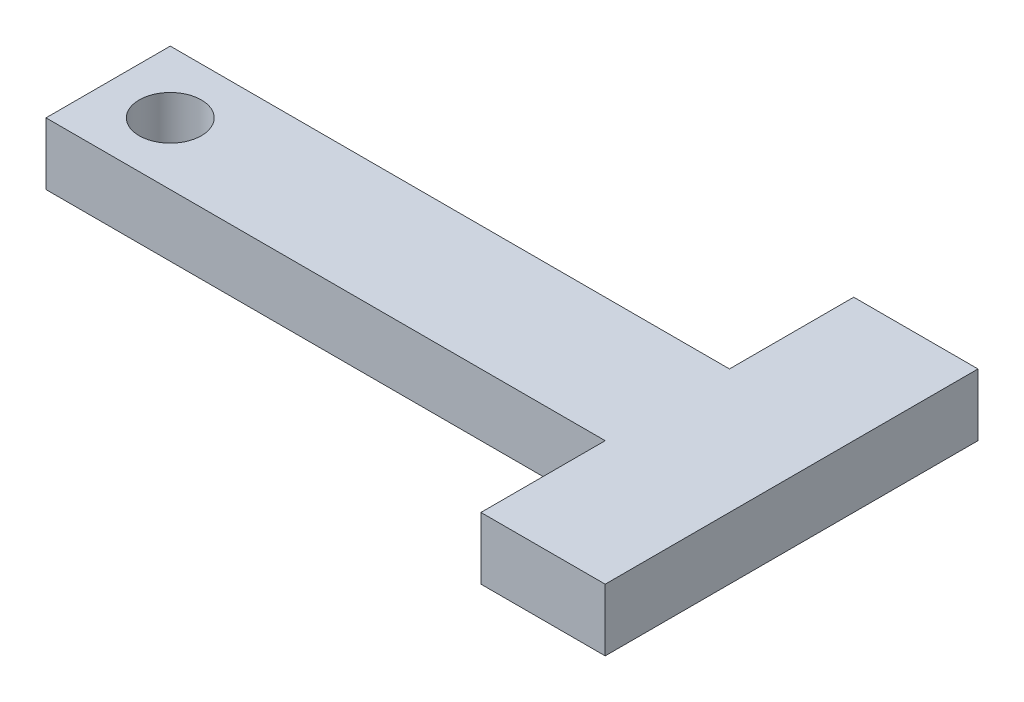
SolidWorks part; units mm, degrees
ref_plane "Front Plane" through (0, 0, 0) normal (0, 0, 1) x (1, 0, 0)
ref_plane "Top Plane" through (0, 0, 0) normal (0, 1, 0) x (1, 0, 0)
ref_plane "Right Plane" through (0, 0, 0) normal (1, 0, 0) x (0, 0, -1)
sketch "Sketch1" plane through (0, 0, 0) normal (0, 1, 0) x (1, 0, 0)
  line L0 (90, 20) -> (90, 40)
  line L1 (0, 0) -> (90, 0)
  line L2 (0, 0) -> (0, 20)
  line L3 (0, 20) -> (90, 20)
  line L4 (90, 40) -> (110, 40)
  line L5 (110, 40) -> (110, -20)
  line L6 (110, -20) -> (90, -20)
  line L7 (90, -20) -> (90, 0)
  circle A0 centre (10, 10) radius 5
  dimension "D5" = 10
  dimension "D1" = 20
  dimension "D2" = 90
  dimension "D3" = 60
  dimension "D4" = 20
  dimension "D6" = 10
  dimension "D7" = 10
extrude "Boss-Extrude1" add sketch "Sketch1" along normal blind 10
